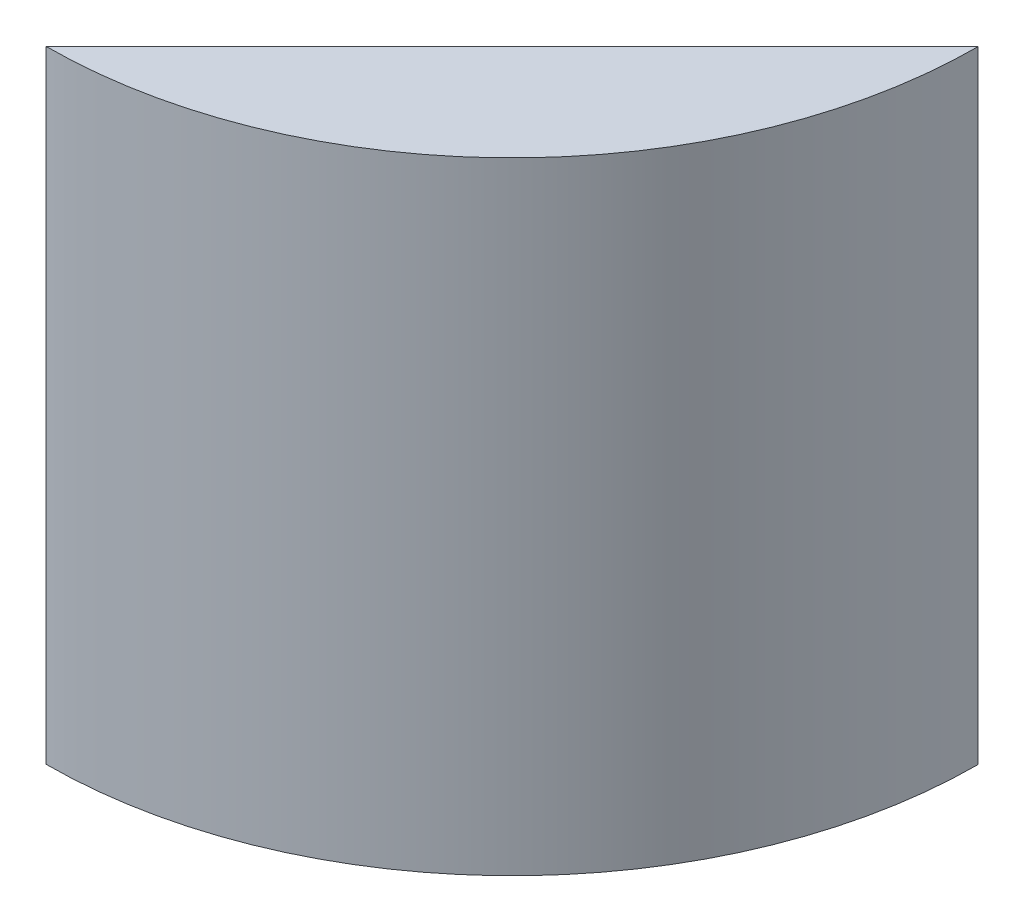
SolidWorks part; units mm, degrees
ref_plane "Front Plane" through (0, 0, 0) normal (0, 0, 1) x (1, 0, 0)
ref_plane "Top Plane" through (0, 0, 0) normal (0, 1, 0) x (1, 0, 0)
ref_plane "Right Plane" through (0, 0, 0) normal (1, 0, 0) x (0, 0, -1)
sketch "Sketch1" plane through (0, 0, 0) normal (0, 1, 0) x (1, 0, 0)
  circle A0 centre (0, 0) radius 85.725
  dimension "D1" = 171.45
extrude "Boss-Extrude1" add sketch "Sketch1" along normal blind 114.3
sketch "Sketch2" plane through (0, 114.3, 0) normal (0, 1, 0) x (1, 0, 0)
  line L0 (85.7249, -0.1067) -> (0, -85.725)
  line L1 (0, -85.725) -> (-45.6275, -96.7194)
  line L6 (-45.6275, -96.7194) -> (-137.4289, 46.1739)
  line L7 (-137.4289, 46.1739) -> (19.1253, 101.9105)
  line L8 (19.1253, 101.9105) -> (109.8339, 30.6005)
  line L9 (109.8339, 30.6005) -> (85.7249, -0.1067)
  circle A0 centre (0, 0) radius 85.725 construction
extrude "Cut-Extrude1" cut sketch "Sketch2" against normal blind 152.4
sketch "Sketch4" plane through (42.8625, 0, 42.9158) normal (-0.7067, 0, -0.7075) x (-0.7075, 0, 0.7067)
  line L1 (60.579, 0) -> (-60.579, 0) construction
  circle A0 centre (40.6185, 93.472) radius 2.7781
  circle A1 centre (-4.8475, 93.472) radius 2.7781
  circle A2 centre (-4.8475, 25.4) radius 2.7781
  circle A3 centre (40.6185, 25.4) radius 2.7781
  dimension "D1" = 25.4
  dimension "D3" = 45.466
  dimension "D2" = 68.072
  dimension "D4" = 68.072
  dimension "D5" = 45.466
extrude "Cut-Extrude2" cut sketch "Sketch4" against normal blind 12.7
sketch "Sketch5" plane through (0, 0, 0) normal (0, -1, 0) x (-1, 0, 0)
  line L2 (-25.1459, -25.1772) -> (-60.579, -60.6544) construction
  line L5 (0, -85.725) -> (-85.7249, -0.1067) construction
  circle A0 centre (-51.8371, -51.9017) radius 6.985
  arc A1 (-85.7249, -0.1067) -> (0, -85.725) centre (0, 0) ccw construction
  point P7 (-42.8625, -42.9158)
  dimension "D1" = 13.97
  dimension "D2" = 12.7
extrude "Cut-Extrude3" cut sketch "Sketch5" against normal blind 6.35
